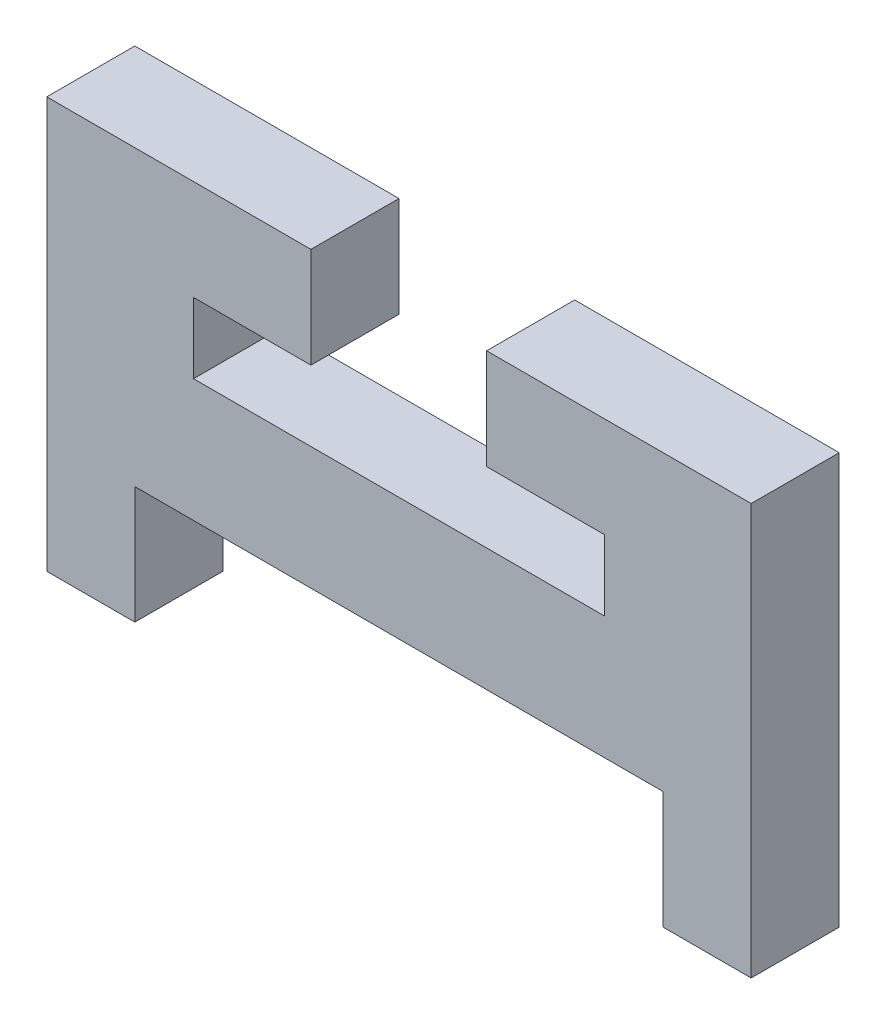
SolidWorks part; units mm, degrees
ref_plane "Alzado" through (0, 0, 0) normal (0, 0, 1) x (1, 0, 0)
ref_plane "Planta" through (0, 0, 0) normal (0, 1, 0) x (1, 0, 0)
ref_plane "Vista lateral" through (0, 0, 0) normal (1, 0, 0) x (0, 0, -1)
sketch "Model" plane through (0, 0, 0) normal (0, 0, 1) x (1, 0, 0)
  line L0 (32.4, 16.3027) -> (25.9, 16.3027)
  line L1 (25.9, 16.3027) -> (25.9, 18.7027)
  line L2 (25.9, 18.7027) -> (29.9, 18.7027)
  line L3 (29.9, 18.7027) -> (29.9, 22.12)
  line L4 (29.9, 22.12) -> (20.9, 22.12)
  line L5 (20.9, 22.12) -> (20.9, 8.12)
  line L6 (20.9, 8.12) -> (23.9, 8.12)
  line L7 (23.9, 8.12) -> (23.9, 12.12)
  line L8 (23.9, 12.12) -> (41.9, 12.12)
  line L9 (41.9, 12.12) -> (41.9, 8.12)
  line L10 (41.9, 8.12) -> (44.9, 8.12)
  line L11 (44.9, 8.12) -> (44.9, 22.12)
  line L12 (44.9, 22.12) -> (35.8864, 22.12)
  line L13 (35.8864, 22.12) -> (35.8864, 18.7027)
  line L14 (35.8864, 18.7027) -> (39.9, 18.7027)
  line L15 (39.9, 18.7027) -> (39.9, 16.3027)
  line L16 (39.9, 16.3027) -> (33.4, 16.3027)
  line L17 (32.4, 16.3027) -> (33.4, 16.3027)
extrude "Saliente-Extruir1" add sketch "Model" along normal blind 3
